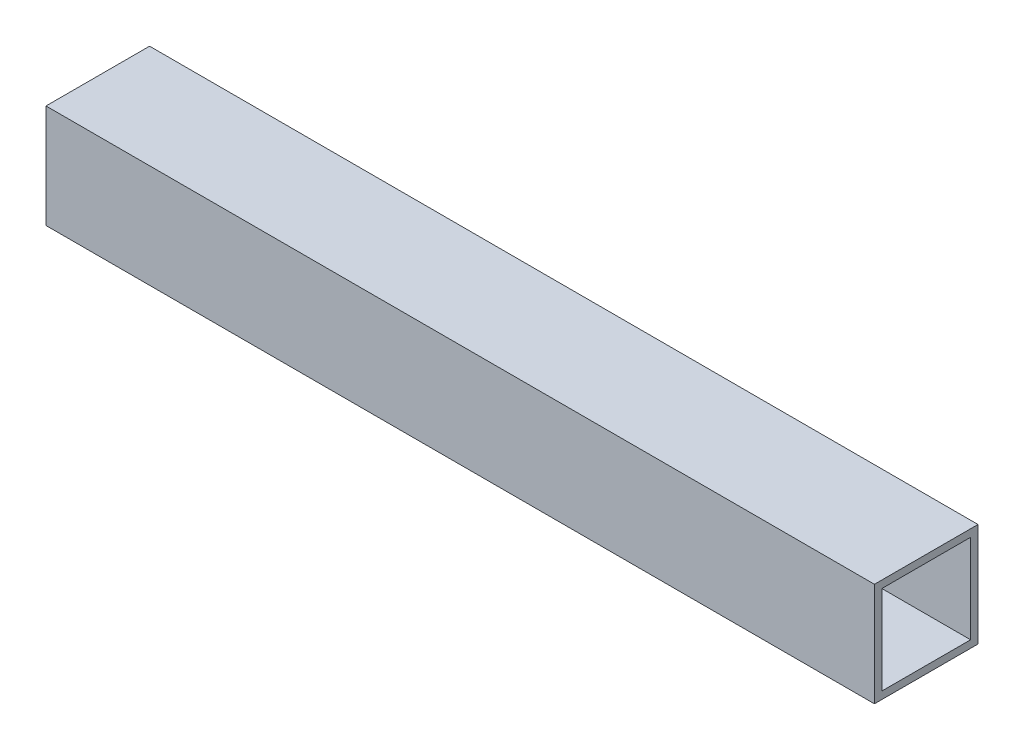
SolidWorks part; units mm, degrees
material "6061 Alloy"
ref_plane "Front Plane" through (0, 0, 0) normal (0, 0, 1) x (1, 0, 0)
ref_plane "Top Plane" through (0, 0, 0) normal (0, 1, 0) x (1, 0, 0)
ref_plane "Right Plane" through (0, 0, 0) normal (1, 0, 0) x (0, 0, -1)
sketch "Sketch1" plane through (0, 0, 0) normal (1, 0, 0) x (0, 0, -1)
  line L0 (41.275, 41.275) -> (3.175, 41.275)
  line L1 (0, 0) -> (44.45, 0)
  line L2 (44.45, 0) -> (44.45, 44.45)
  line L3 (44.45, 44.45) -> (0, 44.45)
  line L4 (0, 44.45) -> (0, 0)
  line L5 (3.175, 41.275) -> (3.175, 3.175)
  line L6 (3.175, 3.175) -> (41.275, 3.175)
  line L7 (41.275, 3.175) -> (41.275, 41.275)
  circle A0 centre (22.225, 22.225) radius 22.225 construction
  dimension "D1" = 44.45
  dimension "D2" = 3.175
extrude "Boss-Extrude1" add sketch "Sketch1" along normal mid plane 355.6
